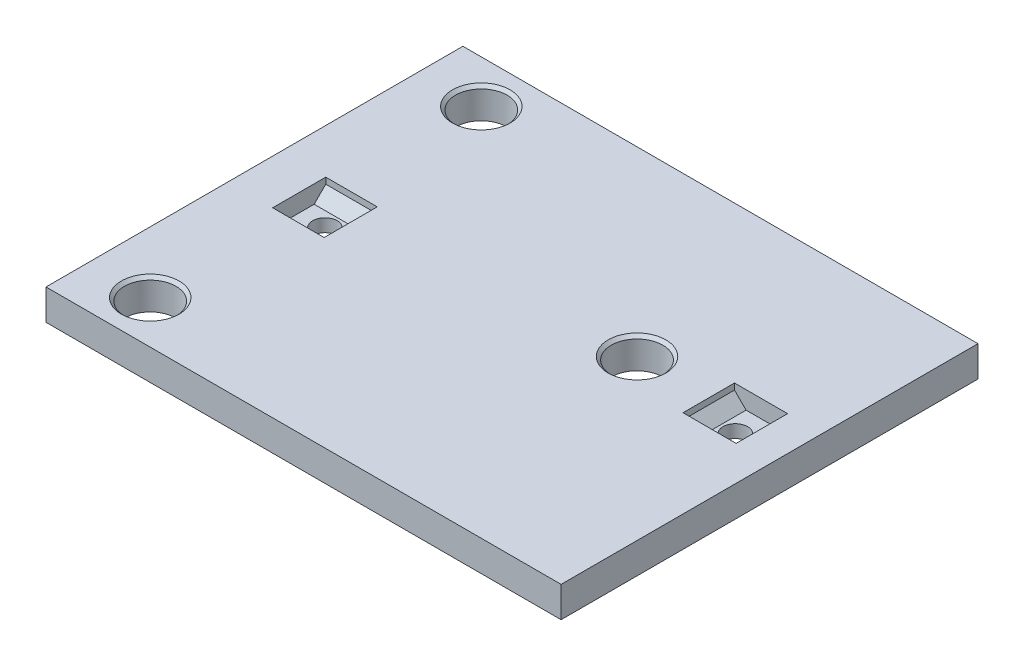
SolidWorks part; units mm, degrees
ref_plane "Front Plane" through (0, 0, 0) normal (0, 0, 1) x (1, 0, 0)
ref_plane "Top Plane" through (0, 0, 0) normal (0, 1, 0) x (1, 0, 0)
ref_plane "Right Plane" through (0, 0, 0) normal (1, 0, 0) x (0, 0, -1)
sketch "Sketch1" plane through (0, 0, 0) normal (0, 1, 0) x (1, 0, 0)
  line L0 (6.35, 53.34) -> (6.35, 33.02) construction
  line L1 (6.35, 33.02) -> (0, 33.02) construction
  line L2 (0, 33.02) -> (0, 0)
  line L3 (0, 0) -> (22.86, 0)
  line L4 (22.86, 0) -> (55.901, 38.5867) construction
  line L5 (55.901, 38.5867) -> (106.701, 38.5867) construction
  line L6 (106.701, 38.5867) -> (106.701, 56.3667)
  line L7 (0, 86.36) -> (0, 53.34)
  line L8 (0, 53.34) -> (6.35, 53.34) construction
  line L9 (0, 86.36) -> (20.32, 86.36)
  line L10 (20.32, 86.36) -> (106.701, 56.3667) construction
  line L11 (12.065, 43.18) -> (6.35, 43.18) construction
  line L12 (0, 53.34) -> (0, 33.02)
  line L13 (22.86, 0) -> (106.701, 0)
  line L14 (106.701, 0) -> (106.701, 38.5867)
  line L15 (20.32, 86.36) -> (106.701, 86.36)
  line L16 (106.701, 86.36) -> (106.701, 56.3667)
  circle A0 centre (14.605, 43.18) radius 2.54
  circle A1 centre (94.0392, 48.7467) radius 2.54
  circle A7 centre (73.681, 48.7467) radius 2.54 construction
  circle A8 centre (12.7, 77.47) radius 2.54 construction
  circle A9 centre (12.7, 8.89) radius 2.54 construction
  point P13 (12.065, 43.18)
  point P18 (94.0392, 46.2067)
  point P19 (0, 0)
  point P55 (11.4163, 0)
  dimension "D10" = 5.08
  dimension "D11" = 5.08
  dimension "D42" = 5.08
  dimension "D43" = 5.08
  dimension "D44" = 5.08
  dimension "D1" = 50.8
  dimension "D2" = 50.8
  dimension "D3" = 22.86
  dimension "D4" = 33.02
  dimension "D5" = 20.32
  dimension "D6" = 20.32
  dimension "D7" = 91.44
  dimension "D8" = 17.78
  dimension "D9" = 6.35
  dimension "D12" = 5.715
  dimension "D13" = 7.62
  dimension "D14" = 79.629
  dimension "D38" = 12.7
  dimension "D39" = 8.89
  dimension "D40" = 8.89
  dimension "D41" = 12.7
  dimension "D45" = 10.16
  dimension "D46" = 33.02
extrude "Boss-Extrude1" add sketch "Sketch1" along normal blind 6.35
sketch "Sketch3" plane through (0, 6.35, 0) normal (0, 1, 0) x (1, 0, 0)
  circle A0 centre (14.605, 43.18) radius 2.54 construction
  circle A1 centre (14.605, 43.18) radius 2.54 construction
  circle A2 centre (94.0392, 48.7467) radius 2.54 construction
  circle A3 centre (94.0392, 48.7467) radius 2.54 construction
  point P4 (14.605, 43.18)
  point P12 (94.0392, 48.7467)
ref_plane "Plane1" through (14.605, 0, 0) normal (-1, 0, 0) x (0, 0, 1)
ref_plane "Plane2" through (0, 0, -48.7467) normal (0, 0, 1) x (1, 0, 0)
sketch "Sketch4" plane through (14.605, 0, 0) normal (-1, 0, 0) x (0, 0, 1)
  line L0 (-46.28, 2.68) -> (-40.08, 2.68)
  line L2 (-37.68, 6.35) -> (-48.68, 6.35)
  line L5 (-43.18, 6.35) -> (-43.18, 2.68) construction
  line L8 (-40.08, 2.68) -> (-40.08, 6.35) construction
  line L9 (-46.28, 2.68) -> (-46.28, 6.35) construction
  line L10 (-46.28, 6.35) -> (-40.08, 2.68) construction
  line L11 (-46.28, 2.68) -> (-40.08, 6.35) construction
  line L12 (-48.68, 6.35) -> (-48.68, 5.08)
  line L13 (-48.68, 5.08) -> (-46.28, 2.68)
  line L14 (-40.08, 2.68) -> (-37.68, 5.08)
  line L15 (-37.68, 5.08) -> (-37.68, 6.35)
  line L16 (-48.68, 5.08) -> (-48.68, 2.68) construction
  line L17 (-48.68, 2.68) -> (-46.28, 2.68) construction
  line L18 (-40.08, 2.68) -> (-37.68, 2.68) construction
  line L19 (-37.68, 2.68) -> (-37.68, 5.08) construction
  point P4 (-40.0286, 0.85)
  dimension "D1" = 1.27
  dimension "D2" = 11
  dimension "D3" = 45
  dimension "D4" = 6.2
extrude "Cut-Extrude1" cut sketch "Sketch4" against normal blind 5.334 and the other way blind 5.334
sketch "Sketch5" plane through (0, 0, -48.7467) normal (0, 0, 1) x (1, 0, 0)
  line L0 (90.9392, 2.68) -> (97.1392, 2.68)
  line L1 (99.5392, 6.35) -> (88.5392, 6.35)
  line L2 (94.0392, 6.35) -> (94.0392, 2.68) construction
  line L3 (97.1392, 2.68) -> (97.1392, 6.35) construction
  line L4 (90.9392, 2.68) -> (90.9392, 6.35) construction
  line L5 (90.9392, 6.35) -> (97.1392, 2.68) construction
  line L6 (90.9392, 2.68) -> (97.1392, 6.35) construction
  line L7 (88.5392, 6.35) -> (88.5392, 5.08)
  line L8 (88.5392, 5.08) -> (90.9392, 2.68)
  line L9 (97.1392, 2.68) -> (99.5392, 5.08)
  line L10 (99.5392, 5.08) -> (99.5392, 6.35)
  line L11 (88.5392, 5.08) -> (88.5392, 2.68) construction
  line L12 (88.5392, 2.68) -> (90.9392, 2.68) construction
  line L13 (97.1392, 2.68) -> (99.5392, 2.68) construction
  line L14 (99.5392, 2.68) -> (99.5392, 5.08) construction
  point P12 (0, 0)
  point P14 (0, 0)
  dimension "D1" = 11
  dimension "D2" = 1.27
  dimension "D3" = 45
  dimension "D4" = 6.2
extrude "Cut-Extrude2" cut sketch "Sketch5" against normal blind 5.334 and the other way blind 5.334
sketch "Sketch6" plane through (0, 0, 0) normal (0, -1, 0) x (1, 0, 0)
  circle A0 centre (12.7, -8.89) radius 5.334
  circle A1 centre (73.681, -48.7467) radius 5.334
  circle A2 centre (12.7, -77.47) radius 5.334
  dimension "D1" = 10.668
  dimension "D2" = 10.668
  dimension "D3" = 10.668
extrude "Cut-Extrude3" cut sketch "Sketch6" against normal through all
chamfer "Chamfer1" distance 0.635 angle 45 3 edges at (12.7, 6.35, -14.224) (73.681, 6.35, -54.0807) (12.7, 6.35, -82.804)
